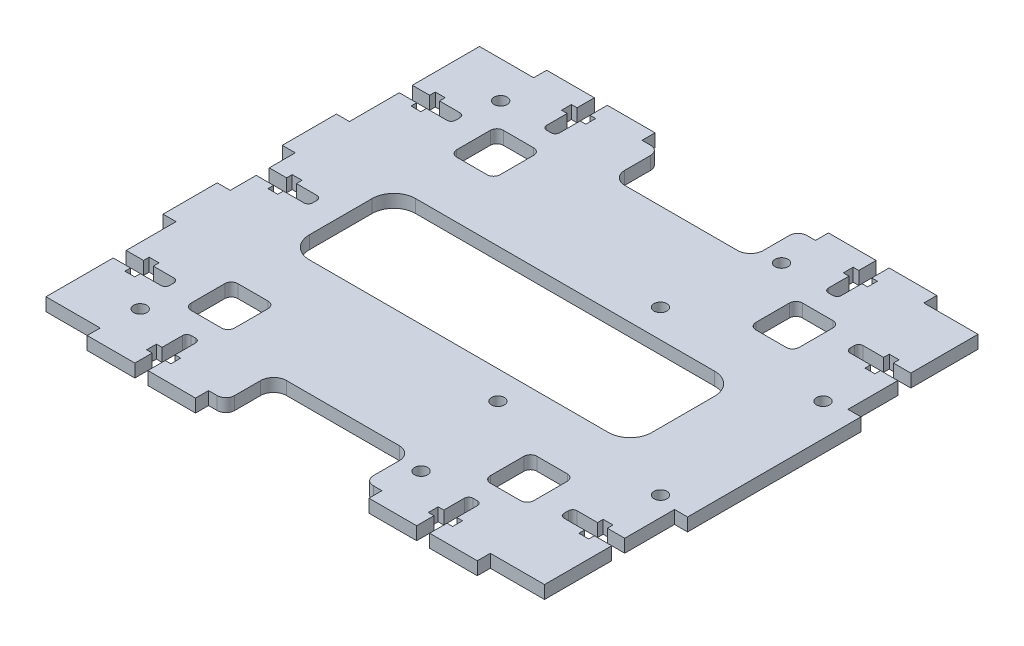
SolidWorks part; units mm, degrees
material "Acrylic (Medium-high impact)"
ref_plane "Plano frontal" through (0, 0, 0) normal (0, 0, 1) x (1, 0, 0)
ref_plane "Plano superior" through (0, 0, 0) normal (0, 1, 0) x (1, 0, 0)
ref_plane "Plano direito" through (0, 0, 0) normal (1, 0, 0) x (0, 0, -1)
sketch "Esboço1" plane through (0, 0, 0) normal (0, 1, 0) x (1, 0, 0)
  line L1 (-57.5, -50) -> (57.5, -50)
  line L2 (-57.5, -50) -> (-57.5, 50)
  line L3 (-57.5, 50) -> (57.5, 50)
  line L4 (57.5, -50) -> (57.5, 50)
  line L5 (-57.5, -50) -> (57.5, 50) construction
  line L6 (-57.5, 50) -> (57.5, -50) construction
  point P0 (0, 0)
  dimension "D1" = 115
  dimension "D2" = 100
extrude "Ressalto-extrusão1" add sketch "Esboço1" along normal mid plane 3
sketch "Esboço4" plane through (0, 1.5, 0) normal (0, 1, 0) x (1, 0, 0)
  line L0 (-57.5, -50) -> (57.5, -50) construction
  line L5 (-57.5, 50) -> (-57.5, -50) construction
  line L6 (-57.5, 20) -> (-60.5, 20)
  line L7 (-57.5, 20) -> (-57.5, -20)
  line L8 (-57.5, -20) -> (-60.5, -20)
  line L9 (-60.5, 20) -> (-60.5, -20)
  line L10 (-45, -50) -> (-20, -50)
  line L15 (-45, -50) -> (-45, -53)
  line L26 (0, -1.65) -> (0, 1.65) construction
  line L27 (60.5, 20) -> (60.5, -20)
  line L28 (57.5, -20) -> (60.5, -20)
  line L29 (57.5, 20) -> (57.5, -20)
  line L30 (57.5, 20) -> (60.5, 20)
  line L31 (-45, -53) -> (-20, -53)
  line L32 (-20, -50) -> (-20, -53)
  line L33 (20, -50) -> (20, -53)
  line L34 (45, -53) -> (20, -53)
  line L35 (45, -50) -> (45, -53)
  line L36 (45, -50) -> (20, -50)
  line L37 (-1.65, 0) -> (1.65, 0) construction
  line L38 (45, 50) -> (20, 50)
  line L39 (45, 50) -> (45, 53)
  line L40 (45, 53) -> (20, 53)
  line L41 (20, 50) -> (20, 53)
  line L42 (-20, 50) -> (-20, 53)
  line L43 (-45, 53) -> (-20, 53)
  line L44 (-45, 50) -> (-45, 53)
  line L45 (-45, 50) -> (-20, 50)
  point P14 (-60.5, 0)
  dimension "D1" = 25
  dimension "D2" = 40
  dimension "D3" = 3
  dimension "D4" = 40
extrude "Ressalto-extrusão2" add sketch "Esboço4" against normal through all
sketch "Esboço2" plane through (0, 1.5, 0) normal (0, 1, 0) x (1, 0, 0)
  line L32 (-45, -53) -> (-20, -53) construction
  line L89 (-34, -53) -> (-31, -53)
  line L90 (-34, -53) -> (-34, -49)
  line L91 (-33, -41) -> (-32, -41)
  line L92 (-31, -53) -> (-31, -49)
  line L93 (-31, -46.73) -> (-29.7, -46.73)
  line L94 (-35.3, -46.73) -> (-34, -46.73)
  line L95 (-35.3, -46.73) -> (-35.3, -49)
  line L96 (-35.3, -49) -> (-34, -49)
  line L97 (-29.7, -46.73) -> (-29.7, -49)
  line L98 (-31, -49) -> (-29.7, -49)
  line L99 (-34, -46.73) -> (-34, -42)
  line L100 (-31, -46.73) -> (-31, -42)
  line L101 (0, -1.65) -> (0, 1.65) construction
  line L102 (31, -46.73) -> (31, -42)
  line L103 (34, -46.73) -> (34, -42)
  line L104 (31, -49) -> (29.7, -49)
  line L105 (29.7, -46.73) -> (29.7, -49)
  line L106 (35.3, -49) -> (34, -49)
  line L107 (35.3, -46.73) -> (35.3, -49)
  line L108 (35.3, -46.73) -> (34, -46.73)
  line L109 (31, -46.73) -> (29.7, -46.73)
  line L110 (31, -53) -> (31, -49)
  line L111 (33, -41) -> (32, -41)
  line L112 (34, -53) -> (34, -49)
  line L113 (34, -53) -> (31, -53)
  line L114 (-1.65, 0) -> (1.65, 0) construction
  line L115 (34, 53) -> (31, 53)
  line L116 (34, 53) -> (34, 49)
  line L117 (33, 41) -> (32, 41)
  line L118 (31, 53) -> (31, 49)
  line L119 (31, 46.73) -> (29.7, 46.73)
  line L120 (35.3, 46.73) -> (34, 46.73)
  line L121 (35.3, 46.73) -> (35.3, 49)
  line L122 (35.3, 49) -> (34, 49)
  line L123 (29.7, 46.73) -> (29.7, 49)
  line L124 (31, 49) -> (29.7, 49)
  line L125 (34, 46.73) -> (34, 42)
  line L126 (31, 46.73) -> (31, 42)
  line L127 (-31, 46.73) -> (-31, 42)
  line L128 (-34, 46.73) -> (-34, 42)
  line L129 (-31, 49) -> (-29.7, 49)
  line L130 (-29.7, 46.73) -> (-29.7, 49)
  line L131 (-35.3, 49) -> (-34, 49)
  line L132 (-35.3, 46.73) -> (-35.3, 49)
  line L133 (-35.3, 46.73) -> (-34, 46.73)
  line L134 (-31, 46.73) -> (-29.7, 46.73)
  line L135 (-31, 53) -> (-31, 49)
  line L136 (-33, 41) -> (-32, 41)
  line L137 (-34, 53) -> (-34, 49)
  line L138 (-34, 53) -> (-31, 53)
  arc A8 (-34, -42) -> (-33, -41) centre (-33, -42) cw
  arc A9 (-32, -41) -> (-31, -42) centre (-32, -42) cw
  arc A10 (32, -41) -> (31, -42) centre (32, -42) ccw
  arc A11 (34, -42) -> (33, -41) centre (33, -42) ccw
  arc A12 (34, 42) -> (33, 41) centre (33, 42) cw
  arc A13 (32, 41) -> (31, 42) centre (32, 42) cw
  arc A14 (-32, 41) -> (-31, 42) centre (-32, 42) ccw
  arc A15 (-34, 42) -> (-33, 41) centre (-33, 42) ccw
  point P6 (-32.5, -53)
  point P7 (-32.5, -53)
  point P18 (-34, -41)
  point P21 (-31, -41)
  point P40 (31, -41)
  point P41 (34, -41)
  point P76 (34, 41)
  point P77 (31, 41)
  point P78 (-31, 41)
  point P79 (-34, 41)
  dimension "D7" = 1
  dimension "D1" = 3
  dimension "D2" = 12
  dimension "D3" = 2.27
  dimension "D4" = 4
  dimension "D5" = 1.3
  dimension "D6" = 1.3
extrude "Corte-extrusão1" cut sketch "Esboço2" against normal through all
sketch "Esboço7" plane through (0, 1.5, 0) normal (0, 1, 0) x (1, 0, 0)
  line L0 (-57.5, -20) -> (-57.5, -50) construction
  line L1 (-57.5, -31.5) -> (-53.5, -31.5)
  line L2 (-57.5, -31.5) -> (-57.5, -34.5)
  line L3 (-57.5, -34.5) -> (-53.5, -34.5)
  line L4 (-45.5, -32.5) -> (-45.5, -33.5)
  line L6 (-53.5, -30.2) -> (-51.23, -30.2)
  line L7 (-53.5, -30.2) -> (-53.5, -31.5)
  line L8 (-53.5, -35.8) -> (-51.23, -35.8)
  line L9 (-51.23, -30.2) -> (-51.23, -31.5)
  line L10 (-51.23, -31.5) -> (-46.5, -31.5)
  line L11 (-51.23, -34.5) -> (-46.5, -34.5)
  line L12 (-51.23, -34.5) -> (-51.23, -35.8)
  line L13 (-53.5, -34.5) -> (-53.5, -35.8)
  line L14 (-60.5, -20) -> (-57.5, -20) construction
  line L15 (0, -1.65) -> (0, 1.65) construction
  line L17 (53.5, -34.5) -> (53.5, -35.8)
  line L18 (51.23, -34.5) -> (51.23, -35.8)
  line L19 (51.23, -34.5) -> (46.5, -34.5)
  line L20 (51.23, -31.5) -> (46.5, -31.5)
  line L21 (51.23, -30.2) -> (51.23, -31.5)
  line L22 (53.5, -35.8) -> (51.23, -35.8)
  line L23 (53.5, -30.2) -> (53.5, -31.5)
  line L24 (53.5, -30.2) -> (51.23, -30.2)
  line L25 (45.5, -32.5) -> (45.5, -33.5)
  line L26 (57.5, -34.5) -> (53.5, -34.5)
  line L27 (57.5, -31.5) -> (57.5, -34.5)
  line L28 (57.5, -31.5) -> (53.5, -31.5)
  line L29 (-1.65, 0) -> (1.65, 0) construction
  line L32 (57.5, 31.5) -> (53.5, 31.5)
  line L33 (57.5, 31.5) -> (57.5, 34.5)
  line L34 (57.5, 34.5) -> (53.5, 34.5)
  line L35 (45.5, 32.5) -> (45.5, 33.5)
  line L36 (53.5, 30.2) -> (51.23, 30.2)
  line L37 (53.5, 30.2) -> (53.5, 31.5)
  line L38 (53.5, 35.8) -> (51.23, 35.8)
  line L39 (51.23, 30.2) -> (51.23, 31.5)
  line L40 (51.23, 31.5) -> (46.5, 31.5)
  line L41 (51.23, 34.5) -> (46.5, 34.5)
  line L42 (51.23, 34.5) -> (51.23, 35.8)
  line L43 (53.5, 34.5) -> (53.5, 35.8)
  line L44 (-53.5, 34.5) -> (-53.5, 35.8)
  line L45 (-51.23, 34.5) -> (-51.23, 35.8)
  line L46 (-51.23, 34.5) -> (-46.5, 34.5)
  line L47 (-51.23, 31.5) -> (-46.5, 31.5)
  line L48 (-51.23, 30.2) -> (-51.23, 31.5)
  line L49 (-53.5, 35.8) -> (-51.23, 35.8)
  line L50 (-53.5, 30.2) -> (-53.5, 31.5)
  line L51 (-53.5, 30.2) -> (-51.23, 30.2)
  line L52 (-45.5, 32.5) -> (-45.5, 33.5)
  line L53 (-57.5, 34.5) -> (-53.5, 34.5)
  line L54 (-57.5, 31.5) -> (-57.5, 34.5)
  line L55 (-57.5, 31.5) -> (-53.5, 31.5)
  arc A0 (46.5, -34.5) -> (45.5, -33.5) centre (46.5, -33.5) cw
  arc A1 (46.5, -31.5) -> (45.5, -32.5) centre (46.5, -32.5) ccw
  arc A2 (45.5, 32.5) -> (46.5, 31.5) centre (46.5, 32.5) ccw
  arc A3 (45.5, 33.5) -> (46.5, 34.5) centre (46.5, 33.5) cw
  arc A4 (-46.5, 34.5) -> (-45.5, 33.5) centre (-46.5, 33.5) cw
  arc A5 (-46.5, 31.5) -> (-45.5, 32.5) centre (-46.5, 32.5) ccw
  arc A6 (-46.5, -31.5) -> (-45.5, -32.5) centre (-46.5, -32.5) cw
  arc A7 (-46.5, -34.5) -> (-45.5, -33.5) centre (-46.5, -33.5) ccw
  point P22 (45.5, -34.5)
  point P68 (45.5, -31.5)
  point P71 (45.5, 31.5)
  point P74 (45.5, 34.5)
  point P77 (-45.5, 34.5)
  point P80 (-45.5, 31.5)
  point P83 (-45.5, -31.5)
  point P86 (-45.5, -34.5)
  dimension "D8" = 1
  dimension "D1" = 3
  dimension "D2" = 12
  dimension "D3" = 2.27
  dimension "D4" = 4
  dimension "D5" = 1.3
  dimension "D6" = 11.5
  dimension "D7" = 1.3
extrude "Corte-extrusão4" cut sketch "Esboço7" against normal through all
sketch "Esboço13" plane through (0, -1.5, 0) normal (0, -1, 0) x (-1, 0, 0)
  line L0 (-15.5, 18.75) -> (-15.5, -18.75) construction
  line L1 (-57.5, 20) -> (-57.5, 31.5) construction
  circle A0 centre (-15.5, -18.75) radius 1.5
  circle A1 centre (-53, -18.75) radius 1.5
  circle A2 centre (-15.5, 18.75) radius 1.5
  circle A3 centre (-53, 18.75) radius 1.5
  point P10 (-15.5, 0)
  dimension "D1" = 3
  dimension "D2" = 3
  dimension "D3" = 37.5
  dimension "D5" = 37.5
extrude "Corte-extrusão8" cut sketch "Esboço13" against normal through all both and the other way through all
sketch "Sketch4" plane through (0, 0, 0) normal (0, 1, 0) x (1, 0, 0)
  line L0 (-1.65, 0) -> (1.65, 0) construction
  line L26 (-45.5, 32.5) -> (-45.5, 33.5) construction
  line L27 (-33, 41) -> (-32, 41) construction
  line L40 (-38, 36) -> (-31, 36)
  line L46 (-39.5, 34.5) -> (-39.5, 26.75)
  line L53 (-38, 25.25) -> (-31, 25.25)
  line L54 (-29.5, 34.5) -> (-29.5, 26.75)
  line L61 (0, -1.65) -> (0, 1.65) construction
  line L62 (29.5, 34.5) -> (29.5, 26.75)
  line L63 (38, 25.25) -> (31, 25.25)
  line L64 (39.5, 34.5) -> (39.5, 26.75)
  line L65 (38, 36) -> (31, 36)
  line L66 (38, -36) -> (31, -36)
  line L67 (39.5, -34.5) -> (39.5, -26.75)
  line L68 (38, -25.25) -> (31, -25.25)
  line L69 (29.5, -34.5) -> (29.5, -26.75)
  line L70 (-29.5, -34.5) -> (-29.5, -26.75)
  line L71 (-38, -25.25) -> (-31, -25.25)
  line L72 (-39.5, -34.5) -> (-39.5, -26.75)
  line L73 (-38, -36) -> (-31, -36)
  arc A31 (-31, 25.25) -> (-29.5, 26.75) centre (-31, 26.75) ccw
  arc A32 (-31, 36) -> (-29.5, 34.5) centre (-31, 34.5) cw
  arc A33 (-38, 36) -> (-39.5, 34.5) centre (-38, 34.5) ccw
  arc A34 (-39.5, 26.75) -> (-38, 25.25) centre (-38, 26.75) ccw
  arc A35 (39.5, 26.75) -> (38, 25.25) centre (38, 26.75) cw
  arc A36 (38, 36) -> (39.5, 34.5) centre (38, 34.5) cw
  arc A37 (31, 36) -> (29.5, 34.5) centre (31, 34.5) ccw
  arc A38 (31, 25.25) -> (29.5, 26.75) centre (31, 26.75) cw
  arc A39 (31, -25.25) -> (29.5, -26.75) centre (31, -26.75) ccw
  arc A40 (31, -36) -> (29.5, -34.5) centre (31, -34.5) cw
  arc A41 (38, -36) -> (39.5, -34.5) centre (38, -34.5) ccw
  arc A42 (39.5, -26.75) -> (38, -25.25) centre (38, -26.75) ccw
  arc A43 (-39.5, -26.75) -> (-38, -25.25) centre (-38, -26.75) cw
  arc A44 (-38, -36) -> (-39.5, -34.5) centre (-38, -34.5) cw
  arc A45 (-31, -36) -> (-29.5, -34.5) centre (-31, -34.5) ccw
  arc A46 (-31, -25.25) -> (-29.5, -26.75) centre (-31, -26.75) cw
  circle A50 centre (53, 18.75) radius 1.5 construction
  dimension "D4" = 6
  dimension "D1" = 10
  dimension "D3" = 5
  dimension "D6" = 1.5
  dimension "D2" = 5
  dimension "D5" = 10
extrude "Cut-Extrude3" cut sketch "Sketch4" against normal through all both and the other way through all
sketch "Sketch5" plane through (0, 0, 0) normal (0, 1, 0) x (1, 0, 0)
  line L18 (-60.5, 20) -> (-60.5, -20) construction
  line L19 (-60.5, 7.5) -> (-57.5, 7.5)
  line L20 (-60.5, 7.5) -> (-60.5, -7.5)
  line L21 (-60.5, -7.5) -> (-57.5, -7.5)
  line L22 (-57.5, 7.5) -> (-57.5, 1.5)
  line L23 (-57.5, -1.5) -> (-57.5, -7.5)
  line L24 (-57.5, 1.5) -> (-53.5, 1.5)
  line L26 (-57.5, -1.5) -> (-53.5, -1.5)
  line L27 (-45.5, 0.5) -> (-45.5, -0.5)
  line L28 (-53.5, 2.8) -> (-51.23, 2.8)
  line L29 (-53.5, 2.8) -> (-53.5, 1.5)
  line L30 (-53.5, -2.8) -> (-51.23, -2.8)
  line L31 (-51.23, 2.8) -> (-51.23, 1.5)
  line L32 (-51.23, 1.5) -> (-46.5, 1.5)
  line L33 (-53.5, -1.5) -> (-53.5, -2.8)
  line L34 (-51.23, -1.5) -> (-51.23, -2.8)
  line L35 (-51.23, -1.5) -> (-46.5, -1.5)
  arc A2 (-46.5, -1.5) -> (-45.5, -0.5) centre (-46.5, -0.5) ccw
  arc A3 (-46.5, 1.5) -> (-45.5, 0.5) centre (-46.5, 0.5) cw
  point P6 (-60.5, 0)
  point P12 (-45.5, 0)
  point P15 (-45.5, -1.5)
  point P18 (-45.5, 1.5)
  dimension "D9" = 1.3
  dimension "D5" = 1
  dimension "D1" = 15
  dimension "D2" = 3
  dimension "D3" = 12
  dimension "D4" = 3
  dimension "D6" = 4
  dimension "D7" = 2.27
  dimension "D8" = 1.3
extrude "Cut-Extrude4" cut sketch "Sketch5" against normal through all both and the other way through all
sketch "Sketch6" plane through (0, 0, 0) normal (0, 1, 0) x (1, 0, 0)
  line L0 (-20, -50) -> (20, -50) construction
  line L1 (-16, -50) -> (16, -50)
  line L2 (-16, -50) -> (-16, -42)
  line L3 (-13, -39) -> (13, -39)
  line L4 (16, -50) -> (16, -42)
  line L5 (-38, -36) -> (-31, -36) construction
  line L6 (-1.65, 0) -> (1.65, 0) construction
  line L7 (16, 50) -> (16, 42)
  line L8 (-13, 39) -> (13, 39)
  line L9 (-16, 50) -> (-16, 42)
  line L10 (-16, 50) -> (16, 50)
  line L11 (20, -50) -> (20, -53) construction
  arc A0 (-16, -42) -> (-13, -39) centre (-13, -42) cw
  arc A1 (13, -39) -> (16, -42) centre (13, -42) cw
  arc A2 (13, 39) -> (16, 42) centre (13, 42) ccw
  arc A3 (-16, 42) -> (-13, 39) centre (-13, 42) ccw
  point P6 (0, -39)
  point P12 (-16, -39)
  point P15 (16, -39)
  point P26 (16, 39)
  point P27 (-16, 39)
  dimension "D2" = 3
  dimension "D1" = 4
  dimension "D3" = 3
extrude "Cut-Extrude5" cut sketch "Sketch6" against normal through all both and the other way through all
fillet "Fillet1" radius 2 4 edges at (16, 0, 50) (-16, 0, 50) (16, 0, -50) (-16, 0, -50)
sketch "Sketch7" plane through (0, 0, 0) normal (0, 1, 0) x (1, 0, 0)
  line L0 (39.5, 26.75) -> (39.5, 34.5) construction
  line L1 (-34.5, -12.25) -> (34.5, -12.25)
  line L2 (-39.5, -7.25) -> (-39.5, 7.25)
  line L3 (-34.5, 12.25) -> (34.5, 12.25)
  line L4 (39.5, -7.25) -> (39.5, 7.25)
  line L5 (0, 12.25) -> (0, -12.25) construction
  line L6 (-39.5, 0) -> (39.5, 0) construction
  circle A1 centre (15.5, 18.75) radius 1.5 construction
  arc A2 (34.5, 12.25) -> (39.5, 7.25) centre (34.5, 7.25) cw
  arc A3 (34.5, -12.25) -> (39.5, -7.25) centre (34.5, -7.25) ccw
  arc A4 (-34.5, -12.25) -> (-39.5, -7.25) centre (-34.5, -7.25) cw
  arc A5 (-39.5, 7.25) -> (-34.5, 12.25) centre (-34.5, 7.25) cw
  point P0 (0, 0)
  dimension "D2" = 5
  dimension "D1" = 5
extrude "Cut-Extrude6" cut sketch "Sketch7" against normal through all both and the other way through all
sketch "Sketch8" plane through (0, 1.5, 0) normal (0, 1, 0) x (1, 0, 0)
  circle A0 centre (-44.2, -41.58) radius 1.5
  circle A1 centre (-44.2, 41.58) radius 1.5
  circle A2 centre (20.6, -41.58) radius 1.5
  circle A3 centre (20.6, 41.58) radius 1.5
  dimension "D1" = 3
extrude "Cut-Extrude7" cut sketch "Sketch8" against normal through all both and the other way through all
